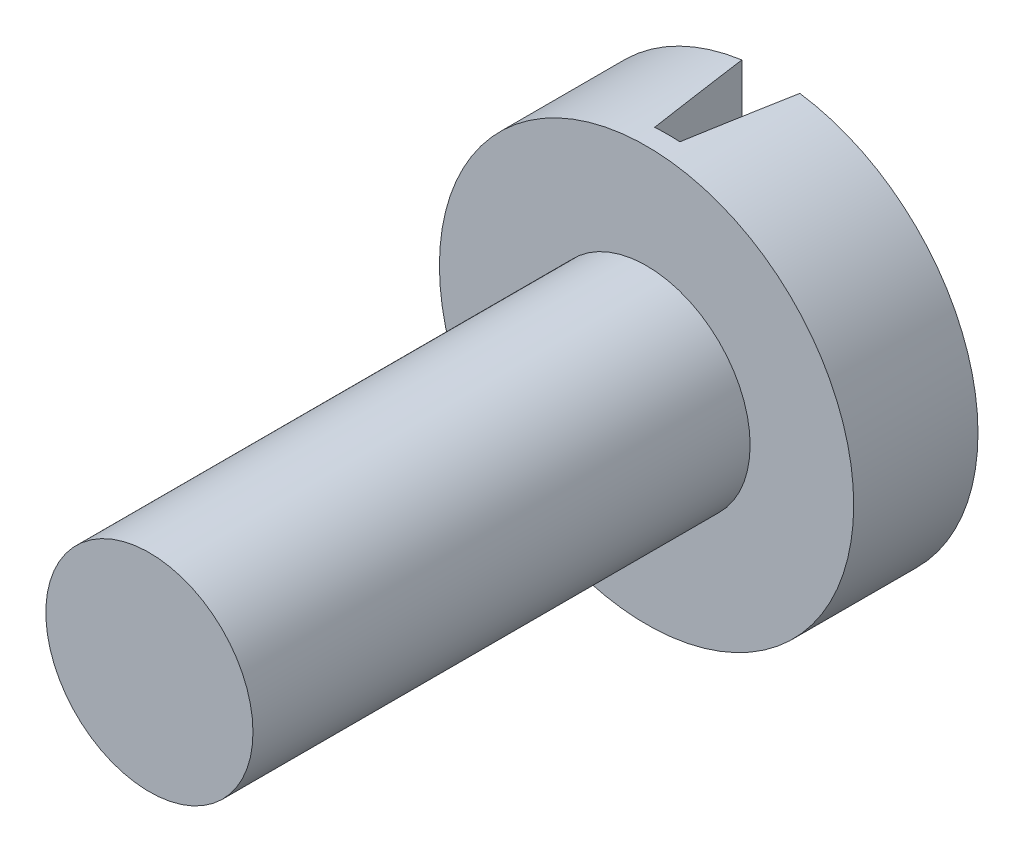
SolidWorks part; units mm, degrees
ref_plane "Alzado" through (0, 0, 0) normal (0, 0, 1) x (1, 0, 0)
ref_plane "Planta" through (0, 0, 0) normal (0, 1, 0) x (1, 0, 0)
ref_plane "Vista lateral" through (0, 0, 0) normal (1, 0, 0) x (0, 0, -1)
sketch "Croquis1" plane through (0, 0, 0) normal (0, 0, 1) x (1, 0, 0)
  circle A0 centre (0, 0) radius 2.5
  dimension "D1" = 5
extrude "Saliente-Extruir1" add sketch "Croquis1" along normal blind 12
sketch "Croquis2" plane through (0, 0, 0) normal (0, 0, 1) x (1, 0, 0)
  circle A0 centre (0, 0) radius 5
  dimension "D1" = 10
extrude "Saliente-Extruir2" add sketch "Croquis2" against normal blind 3
sketch "Croquis3" plane through (0, 0, -3) normal (0, 0, -1) x (-1, 0, 0)
  line L0 (0, 5) -> (0, -5) construction
  line L2 (-0.7, -5.5) -> (0.7, -5.5)
  line L3 (-0.7, -5.5) -> (-0.7, 5.5)
  line L4 (-0.7, 5.5) -> (0.7, 5.5)
  line L5 (0.7, -5.5) -> (0.7, 5.5)
  line L6 (-0.7, -5.5) -> (0.7, 5.5) construction
  line L7 (-0.7, 5.5) -> (0.7, -5.5) construction
  circle A0 centre (0, 0) radius 5 construction
  point P5 (0, 0)
  dimension "D1" = 1.4
  dimension "D2" = 11
extrude "Cortar-Extruir2" cut sketch "Croquis3" against normal blind 2.5 draft 9
